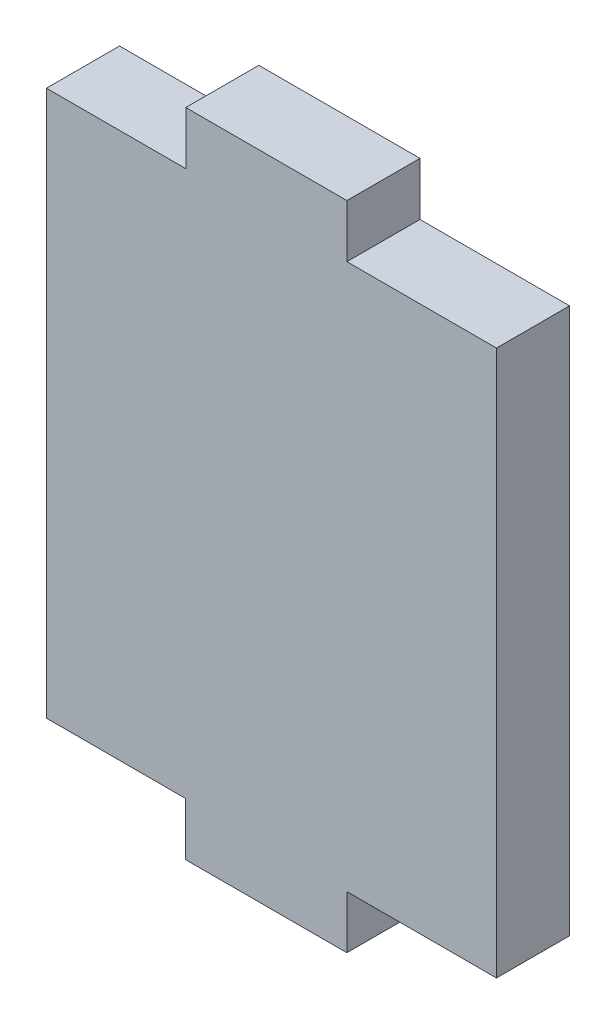
SolidWorks part; units mm, degrees
ref_plane "Front Plane" through (0, 0, 0) normal (0, 0, 1) x (1, 0, 0)
ref_plane "Top Plane" through (0, 0, 0) normal (0, 1, 0) x (1, 0, 0)
ref_plane "Right Plane" through (0, 0, 0) normal (1, 0, 0) x (0, 0, -1)
sketch "Sketch1" plane through (0, 0, 0) normal (0, 0, 1) x (1, 0, 0)
  line L1 (0, 0) -> (20, 0)
  line L2 (0, 0) -> (0, 23.7)
  line L3 (0, 23.7) -> (20, 23.7)
  line L4 (20, 0) -> (20, 23.7)
extrude "Boss-Extrude1" add sketch "Sketch1" along normal blind 3.175
sketch "Sketch2" plane through (0, 0, 3.175) normal (0, 0, 1) x (1, 0, 0)
  line L0 (20, 23.7) -> (0, 23.7) construction
  line L1 (6.5021, 23.7) -> (13.5021, 23.7)
  line L2 (6.5021, 23.7) -> (6.5021, 26)
  line L3 (6.5021, 26) -> (13.5021, 26)
  line L4 (13.5021, 23.7) -> (13.5021, 26)
  line L5 (0, 0) -> (20, 0) construction
  line L6 (6.5, 0) -> (13.5, 0)
  line L7 (6.5, 0) -> (6.5, -2.3)
  line L8 (6.5, -2.3) -> (13.5, -2.3)
  line L9 (13.5, 0) -> (13.5, -2.3)
  line L10 (0, 23.7) -> (0, 0) construction
  line L11 (20, 0) -> (20, 23.7) construction
  dimension "D1" = 7
  dimension "D2" = 2.3
  dimension "D3" = 2.3
  dimension "D4" = 7
  dimension "D5" = 6.5021
  dimension "D6" = 6.4979
  dimension "D7" = 6.5
extrude "Boss-Extrude2" add sketch "Sketch2" against normal blind 3.175
sketch "Sketch3" plane through (0, 0, 3.175) normal (0, 0, 1) x (1, 0, 0)
  line L5 (0, 0) -> (6.5, 0) construction
  line L12 (0, 0) -> (0.45, 0)
  line L15 (0, 23.7) -> (0.45, 23.7)
  line L16 (0, 23.7) -> (0, 0)
  line L18 (0.45, 23.7) -> (0.45, 0)
extrude "Cut-Extrude1" cut sketch "Sketch3" against normal blind 10
